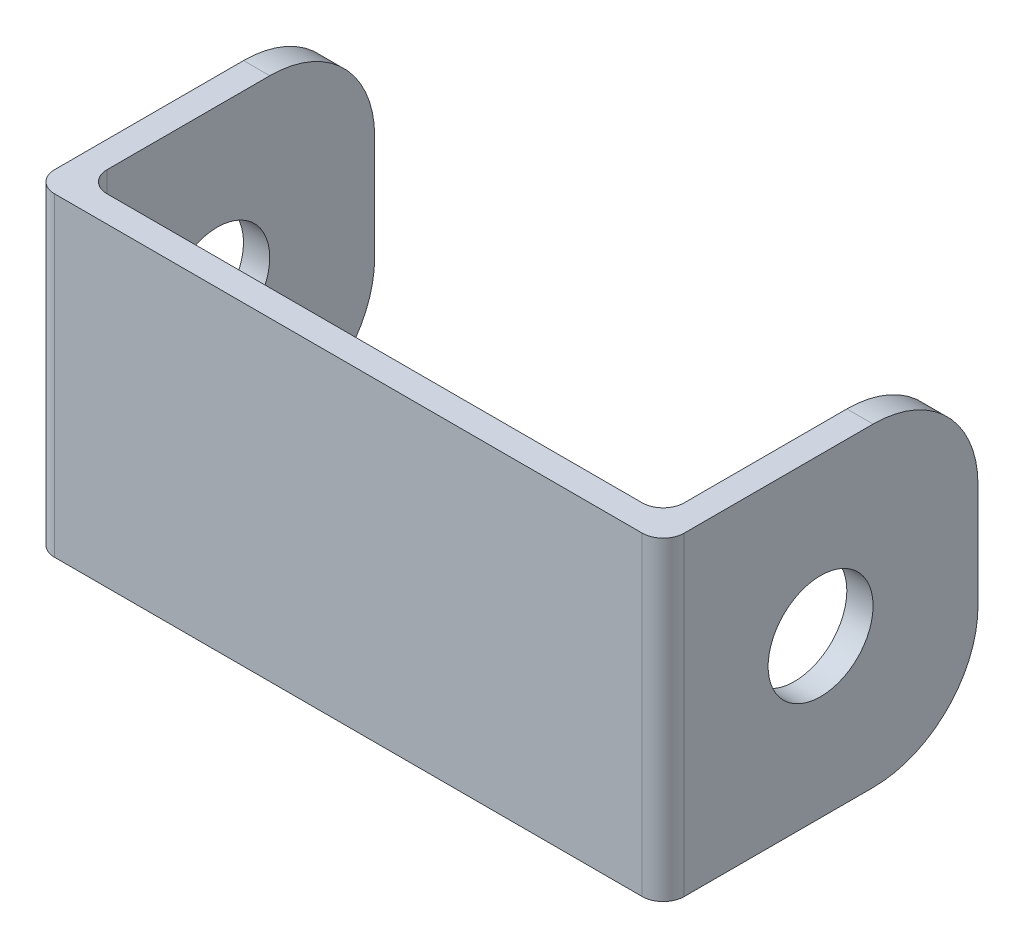
SolidWorks part; units mm, degrees
ref_plane "Front Plane" through (0, 0, 0) normal (0, 0, 1) x (1, 0, 0)
ref_plane "Top Plane" through (0, 0, 0) normal (0, 1, 0) x (1, 0, 0)
ref_plane "Right Plane" through (0, 0, 0) normal (1, 0, 0) x (0, 0, -1)
sketch "Sketch1" plane through (0, 0, 0) normal (0, 1, 0) x (1, 0, 0)
  line L0 (-5.5563, 27.9797) -> (-5.5563, -10.1203)
  line L1 (-5.5563, -10.1203) -> (70.6437, -10.1203)
  line L2 (70.6437, -10.1203) -> (70.6437, 27.9797)
  line L3 (70.6437, 27.9797) -> (67.4687, 27.9797)
  line L4 (67.4687, 27.9797) -> (67.4688, -6.9453)
  line L5 (67.4688, -6.9453) -> (-2.3812, -6.9453)
  line L6 (-2.3812, -6.9453) -> (-2.3813, 27.9797)
  line L7 (-2.3813, 27.9797) -> (-5.5563, 27.9797)
  dimension "D1" = 3.175
  dimension "D2" = 3.175
  dimension "D3" = 69.85
  dimension "D4" = 38.1
extrude "Boss-Extrude1" add sketch "Sketch1" along normal blind 38.1
sketch "Sketch4" plane through (70.6437, 0, 0) normal (1, 0, 0) x (0, 0, -1)
  line L0 (8.9297, 38.1) -> (8.9297, 0) construction
  line L1 (-10.1203, 19.05) -> (27.5672, 19.05) construction
  circle A0 centre (8.9297, 19.05) radius 6.35
  dimension "D1" = 12.7
extrude "Cut-Extrude1" cut sketch "Sketch4" against normal through all
fillet "Fillet1" radius 12.7 4 edges at (-3.9688, 38.1, -27.9797) (-3.9688, 0, -27.9797) (69.0562, 0, -27.9797) (69.0562, 38.1, -27.9797)
fillet "Fillet2" radius 2.54 4 edges at (70.6437, 19.05, 10.1203) (-5.5563, 19.05, 10.1203) (-2.3812, 19.05, 6.9453) (67.4688, 19.05, 6.9453)
sketch "Sketch7" plane through (0, 0, 10.1203) normal (0, 0, 1) x (1, 0, 0)
  line L0 (32.5437, 0) -> (32.5437, 38.1) construction
  line L1 (-3.0163, 0) -> (68.1037, 0) construction
  line L2 (-3.0163, 38.1) -> (68.1037, 38.1) construction
  line L3 (68.1037, 19.05) -> (-3.0163, 19.05) construction
  line L4 (68.1037, 0) -> (68.1037, 38.1) construction
  line L5 (-3.0163, 38.1) -> (-3.0163, 0) construction
